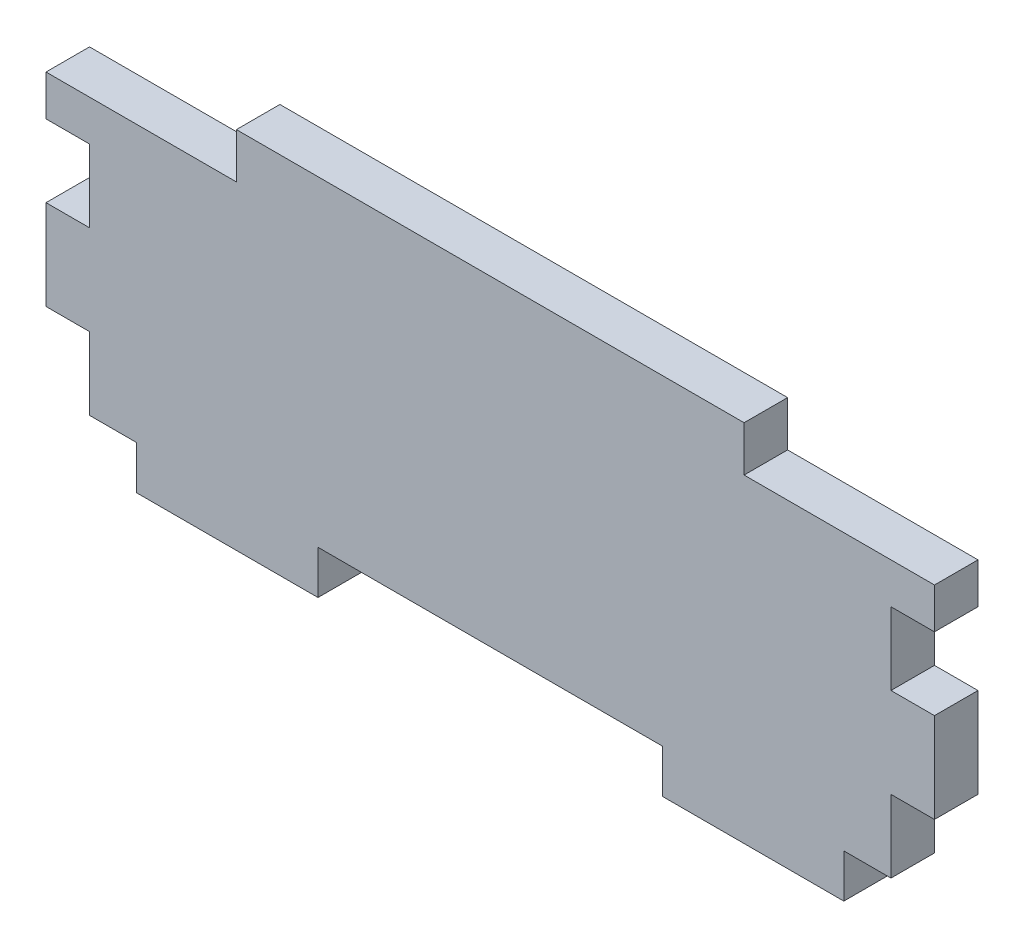
SolidWorks part; units mm, degrees
ref_plane "Front Plane" through (0, 0, 0) normal (0, 0, 1) x (1, 0, 0)
ref_plane "Top Plane" through (0, 0, 0) normal (0, 1, 0) x (1, 0, 0)
ref_plane "Right Plane" through (0, 0, 0) normal (1, 0, 0) x (0, 0, -1)
sketch "Sketch1" plane through (0, 0, 0) normal (0, 0, 1) x (1, 0, 0)
  line L0 (3.048, 9.8044) -> (0, 9.8044) construction
  line L1 (3.048, 16.1036) -> (3.048, 9.8044) construction
  line L2 (3.048, 16.1036) -> (0, 16.1036) construction
  line L3 (0, 21.1836) -> (0, 16.1036) construction
  line L4 (3.048, 21.1836) -> (0, 21.1836) construction
  line L5 (3.048, 24.0284) -> (3.048, 21.1836) construction
  line L7 (3.048, 9.8044) -> (0, 9.8044)
  line L8 (3.048, 16.1036) -> (3.048, 9.8044)
  line L9 (3.048, 16.1036) -> (0, 16.1036)
  line L10 (0, 21.1836) -> (0, 16.1036)
  line L11 (3.048, 21.1836) -> (0, 21.1836)
  line L12 (3.048, 24.0284) -> (3.048, 21.1836)
  line L13 (0, 9.8044) -> (0, 4.7244)
  line L14 (3.048, 24.0284) -> (-10.287, 24.0284)
  line L15 (-10.287, 24.0284) -> (-10.287, 27.2034)
  line L16 (-10.287, 27.2034) -> (-45.847, 27.2034)
  line L17 (-45.847, 27.2034) -> (-45.847, 24.0284)
  line L18 (-45.847, 24.0284) -> (-59.182, 24.0284)
  line L19 (-28.067, 27.2034) -> (-28.067, 4.7244) construction
  line L20 (-56.134, 9.8044) -> (-56.134, 4.7244)
  line L21 (-59.182, 24.0284) -> (-59.182, 21.1836)
  line L22 (-59.182, 21.1836) -> (-56.134, 21.1836)
  line L23 (-56.134, 21.1836) -> (-56.134, 16.1036)
  line L24 (-59.182, 16.1036) -> (-56.134, 16.1036)
  line L25 (-59.182, 16.1036) -> (-59.182, 9.8044)
  line L26 (-59.182, 9.8044) -> (-56.134, 9.8044)
  line L27 (0, 4.7244) -> (-3.302, 4.7244)
  line L28 (-3.302, 4.7244) -> (-3.302, 1.6764)
  line L29 (-3.302, 1.6764) -> (-16.002, 1.6764)
  line L30 (-16.002, 1.6764) -> (-16.002, 4.7244)
  line L31 (-16.002, 4.7244) -> (-40.132, 4.7244)
  line L32 (-40.132, 4.7244) -> (-40.132, 1.6764)
  line L33 (-40.132, 1.6764) -> (-52.832, 1.6764)
  line L34 (-52.832, 1.6764) -> (-52.832, 4.7244)
  line L35 (-52.832, 4.7244) -> (-56.134, 4.7244)
  dimension "D1" = 56.134
  dimension "D2" = 35.56
  dimension "D3" = 3.175
  dimension "D4" = 16.002
  dimension "D5" = 16.002
  dimension "D6" = 3.048
  dimension "D7" = 12.7
extrude "Boss-Extrude1" add sketch "Sketch1" along normal blind 3.048
